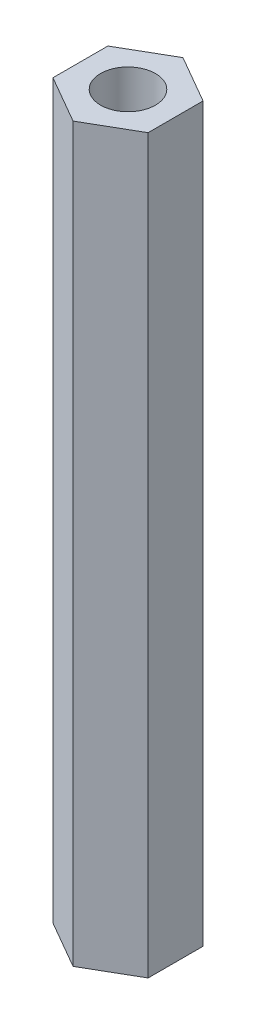
SolidWorks part; units mm, degrees
ref_plane "Front Plane" through (0, 0, 0) normal (0, 0, 1) x (1, 0, 0)
ref_plane "Top Plane" through (0, 0, 0) normal (0, 1, 0) x (1, 0, 0)
ref_plane "Right Plane" through (0, 0, 0) normal (1, 0, 0) x (0, 0, -1)
sketch "Sketch1" plane through (0, 0, 0) normal (0, 1, 0) x (1, 0, 0)
  line L0 (0, 0) -> (2.6, 0) construction
  line L1 (0, 3.0022) -> (-2.6, 1.5011)
  line L2 (-2.6, 1.5011) -> (-2.6, -1.5011)
  line L3 (-2.6, -1.5011) -> (0, -3.0022)
  line L4 (0, -3.0022) -> (2.6, -1.5011)
  line L5 (2.6, -1.5011) -> (2.6, 1.5011)
  line L6 (2.6, 1.5011) -> (0, 3.0022)
  circle A0 centre (0, 0) radius 1.5
  circle A1 centre (0, 0) radius 2.6 construction
  dimension "D1" = 3
  dimension "D2" = 2.6
extrude "Boss-Extrude2" add sketch "Sketch1" along normal blind 40
